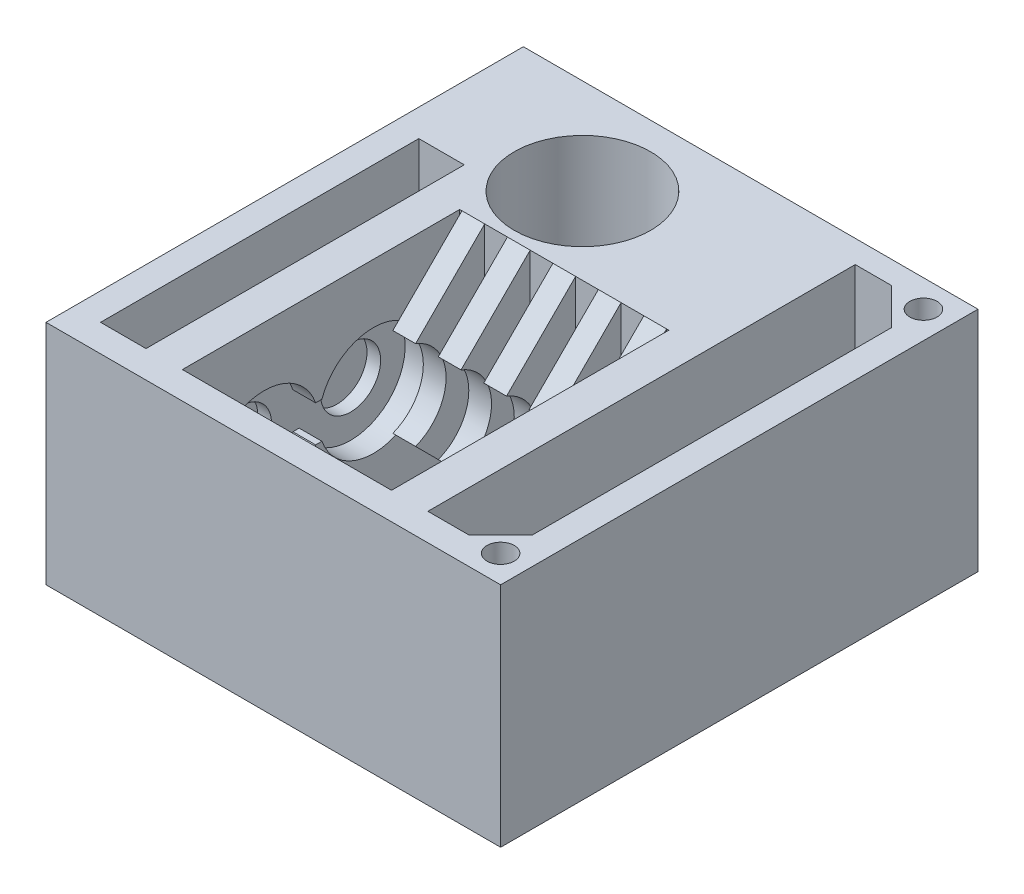
SolidWorks part; units mm, degrees
ref_plane "Front Plane" through (0, 0, 0) normal (0, 0, 1) x (1, 0, 0)
ref_plane "Top Plane" through (0, 0, 0) normal (0, 1, 0) x (1, 0, 0)
ref_plane "Right Plane" through (0, 0, 0) normal (1, 0, 0) x (0, 0, -1)
sketch "Sketch2" plane through (0, 0, 0) normal (0, 1, 0) x (1, 0, 0)
  line L0 (0, 54.9293) -> (0, -74.9036) construction
  line L1 (-50, 52.5) -> (50, 52.5)
  line L2 (-50, 52.5) -> (-50, -52.5)
  line L3 (-50, -52.5) -> (50, -52.5)
  line L4 (50, 52.5) -> (50, -52.5)
  line L5 (-72.7442, 0) -> (103.5154, 0) construction
  dimension "D1" = 105
  dimension "D2" = 100
extrude "Boss-Extrude1" add sketch "Sketch2" along normal blind 50
sketch "Sketch3" plane through (0, 50, 0) normal (0, 1, 0) x (1, 0, 0)
  line L0 (-69.2782, 0) -> (105.7343, 0) construction
  line L1 (0, 63.7563) -> (0, -72.2212) construction
  line L3 (-50, 52.5) -> (-50, -52.5) construction
  line L4 (50, 52.5) -> (-50, 52.5) construction
  circle A0 centre (-39, 0) radius 5 construction
  circle A1 centre (-39, 0) radius 39 construction
  circle A2 centre (-16.0054, 31.5) radius 15
  point P16 (-6.9479, 52.5)
  dimension "D1" = 10
  dimension "D2" = 6
  dimension "D3" = 78
  dimension "D4" = 30
  dimension "D5" = 6
  dimension "D6" = 33.9946
  dimension "D7" = 21
extrude "Cut-Extrude1" cut sketch "Sketch3" against normal up to next
sketch "Sketch5" plane through (0, 50, 0) normal (0, 1, 0) x (1, 0, 0)
  line L0 (50, -52.5) -> (50, 52.5) construction
  line L1 (28, 33.5) -> (44, 33.5)
  line L2 (28, 33.5) -> (28, -46.5)
  line L3 (28, -46.5) -> (44, -46.5)
  line L4 (44, 33.5) -> (44, -46.5)
  line L5 (-44, 23.5) -> (-34, 23.5)
  line L6 (-44, 23.5) -> (-44, -46.5)
  line L7 (-44, -46.5) -> (-34, -46.5)
  line L8 (-34, 23.5) -> (-34, -46.5)
  line L9 (-50, -52.5) -> (50, -52.5) construction
  line L10 (-50, 52.5) -> (-50, -52.5) construction
  dimension "D1" = 6
  dimension "D2" = 6
  dimension "D3" = 80
  dimension "D4" = 16
  dimension "D5" = 6
  dimension "D6" = 6
  dimension "D7" = 70
  dimension "D8" = 10
extrude "Cut-Extrude3" cut sketch "Sketch5" against normal up to next
sketch "Sketch6" plane through (28, 0, 0) normal (1, 0, 0) x (0, 0, -1)
  line L0 (-16.5, 56.9811) -> (-16.5, -19.2113) construction
  line L1 (-69.1636, 25) -> (71.5534, 25) construction
  line L2 (-17.1863, 29) -> (-15.8137, 29)
  line L3 (-17.1863, 21) -> (-15.8137, 21)
  line L4 (-46.5, 0) -> (33.5, 0)
  line L5 (33.5, 0) -> (33.5, 50)
  line L6 (33.5, 50) -> (-46.5, 50)
  line L7 (-46.5, 50) -> (-46.5, 0)
  line L8 (-46.5, 0) -> (33.5, 0) construction
  line L9 (33.5, 0) -> (33.5, 50) construction
  line L10 (33.5, 50) -> (-46.5, 50) construction
  line L11 (-46.5, 50) -> (-46.5, 0) construction
  arc A0 (-17.1863, 29) -> (-17.1863, 21) centre (-28.5, 25) ccw
  circle A2 centre (-28.5, 25) radius 9 construction
  arc A3 (-15.8137, 29) -> (-15.8137, 21) centre (-4.5, 25) cw
  arc A4 (-16.5, 25) -> (-17.1863, 29) centre (-28.5, 25) ccw construction
  arc A5 (-17.1863, 21) -> (-16.5, 25) centre (-28.5, 25) ccw construction
  arc A6 (-15.8137, 21) -> (-16.5, 25) centre (-4.5, 25) cw construction
  arc A7 (-16.5, 25) -> (-15.8137, 29) centre (-4.5, 25) cw construction
  dimension "D4" = 24
  dimension "D5" = 18
  dimension "D2" = 30
  dimension "D3" = 25
  dimension "D6" = 12
  dimension "D7" = 12
  dimension "D8" = 4
  dimension "D1" = 0
extrude "Cut-Extrude4" cut sketch "Sketch6" against normal blind 31
sketch "Sketch7" plane through (28, 0, 0) normal (1, 0, 0) x (0, 0, -1)
  line L0 (-17.1863, 21) -> (-15.8137, 21) construction
  line L1 (-15.8137, 29) -> (-17.1863, 29) construction
  line L2 (-17.1863, 21) -> (-15.8137, 21)
  line L3 (-15.8137, 29) -> (-17.1863, 29)
  arc A6 (-15.8137, 21) -> (-15.8137, 29) centre (-4.5, 25) ccw construction
  arc A7 (-17.1863, 29) -> (-17.1863, 21) centre (-28.5, 25) ccw construction
  arc A8 (-15.8137, 21) -> (-15.8137, 29) centre (-4.5, 25) ccw
  arc A9 (-17.1863, 29) -> (-17.1863, 21) centre (-28.5, 25) ccw
  circle A10 centre (-28.5, 25) radius 6.6
  circle A11 centre (-4.5, 25) radius 6.6
  dimension "D1" = 13.2
  dimension "D2" = 13.2
extrude "Boss-Extrude2" add sketch "Sketch7" against normal blind 3
ref_plane "Plane1" through (-3, 0, 0) normal (1, 0, 0) x (0, 0, -1)
mirror "Mirror1" about plane through (-3, 0, 0) normal (1, 0, 0) of "Boss-Extrude2", "Cut-Extrude4"
sketch "Sketch11" plane through (0, 50, 0) normal (0, 1, 0) x (1, 0, 0)
  line L0 (50, 52.5) -> (-50, 52.5) construction
  line L1 (28, 47.5) -> (44, 47.5)
  line L2 (28, 47.5) -> (28, 33.5)
  line L3 (28, 33.5) -> (44, 33.5)
  line L4 (44, 47.5) -> (44, 33.5)
  line L5 (44, -46.5) -> (44, 33.5) construction
  line L6 (28, 33.5) -> (28, -46.5) construction
  line L7 (44, 33.5) -> (28, 33.5) construction
  dimension "D1" = 5
extrude "Cut-Extrude7" cut sketch "Sketch11" against normal up to next
sketch "Sketch8" plane through (0, 50, 0) normal (0, 1, 0) x (1, 0, 0)
  line L0 (28, 47.5) -> (28, -46.5) construction
  line L1 (-26, 14.5) -> (20, 14.5)
  line L2 (-26, 14.5) -> (-26, -46.5)
  line L3 (-26, -46.5) -> (20, -46.5)
  line L4 (20, 14.5) -> (20, -46.5)
  line L5 (-34, -46.5) -> (-34, 23.5) construction
  line L6 (-50, -52.5) -> (50, -52.5) construction
  circle A0 centre (-16.0054, 31.5) radius 15 construction
  dimension "D4" = 2
  dimension "D1" = 8
  dimension "D2" = 8
  dimension "D3" = 6
extrude "Cut-Extrude5" cut sketch "Sketch8" against normal up to next
sketch "Sketch9" plane through (28, 0, 0) normal (1, 0, 0) x (0, 0, -1)
  line L0 (-15.8137, 29) -> (-17.1863, 29) construction
  line L1 (-17.1863, 21) -> (-15.8137, 21) construction
  line L2 (-28.5, 25) -> (60.6587, 25) construction
  line L3 (-15.8137, 29) -> (-17.1863, 29) construction
  line L4 (19.5, 55.6457) -> (19.5, -7.192) construction
  line L5 (-46.5, 0) -> (47.5, 0)
  line L6 (47.5, 0) -> (47.5, 50)
  line L7 (47.5, 50) -> (-46.5, 50)
  line L12 (-46.5, 50) -> (-46.5, 0)
  line L16 (-46.5, 50) -> (-46.5, 0) construction
  line L17 (-17.1863, 21) -> (-15.8137, 21) construction
  line L18 (52.5, 50) -> (52.5, 0) construction
  line L21 (47.5, 0) -> (47.5, 50) construction
  arc A1 (-17.1863, 29) -> (-17.1863, 21) centre (-28.5, 25) ccw construction
  circle A7 centre (19.5, 25) radius 12 construction
  arc A15 (-15.8137, 21) -> (-15.8137, 29) centre (-4.5, 25) ccw construction
  arc A16 (-17.1863, 29) -> (-17.1863, 21) centre (-28.5, 25) ccw construction
  arc A17 (-15.8137, 21) -> (-15.8137, 29) centre (-4.5, 25) ccw construction
  circle A18 centre (19.5, 25) radius 1.75
  dimension "D2" = 24
  dimension "D3" = 3.5
  dimension "D4" = 33
  dimension "D1" = 0
extrude "Cut-Extrude8" cut sketch "Sketch9" against normal blind 3
sketch "Sketch13" plane through (0, 0, 0) normal (0, -1, 0) x (1, 0, 0)
  line L0 (-62.8638, -19.5) -> (95.3177, -19.5) construction
  line L1 (5, -14.5) -> (25, -14.5)
  line L2 (5, -14.5) -> (5, -33.5)
  line L3 (5, -33.5) -> (25, -33.5)
  line L4 (25, -14.5) -> (25, -33.5)
  line L5 (50, -52.5) -> (-50, -52.5) construction
  line L6 (28, 46.5) -> (28, -47.5) construction
  dimension "D1" = 19
  dimension "D2" = 20
  dimension "D3" = 33
  dimension "D4" = 5
  dimension "D5" = 3
extrude "Cut-Extrude9" cut sketch "Sketch13" against normal blind 30
ref_plane "Plane2" through (19.5, 0, 0) normal (-1, 0, 0) x (0, 0, 1)
sketch "Sketch14" plane through (19.5, 0, 0) normal (-1, 0, 0) x (0, 0, 1)
  line L0 (-14.5, 50) -> (-14.5, 0)
  line L1 (-14.5, 0) -> (0.7085, 15.2085)
  line L2 (-19.4881, 25) -> (76.5209, 25) construction
  line L3 (-14.5, 50) -> (0.7085, 34.7915)
  line L5 (-14.5, 0) -> (46.5, 0)
  line L6 (46.5, 0) -> (46.5, 50)
  line L7 (46.5, 50) -> (-14.5, 50)
  line L8 (-14.5, 50) -> (-14.5, 30)
  line L9 (-14.5, 30) -> (-14.5, 0)
  line L10 (-14.5, 0) -> (46.5, 0) construction
  line L11 (46.5, 0) -> (46.5, 50) construction
  line L12 (46.5, 50) -> (-14.5, 50) construction
  line L13 (-14.5, 50) -> (-14.5, 30) construction
  line L14 (-14.5, 30) -> (-14.5, 0) construction
  circle A0 centre (4.5, 25) radius 6.6 construction
  circle A1 centre (4.5, 25) radius 6.6 construction
  arc A2 (0.7085, 34.7915) -> (0.7085, 15.2085) centre (4.5, 25) ccw
  circle A3 centre (28.5, 25) radius 6.6 construction
  circle A4 centre (28.5, 25) radius 6.6 construction
  circle A5 centre (28.5, 25) radius 10 construction
  arc A6 (15, 25) -> (0.7085, 34.7915) centre (4.5, 25) ccw construction
  arc A7 (0.7085, 15.2085) -> (15, 25) centre (4.5, 25) ccw construction
  dimension "D2" = 21
  dimension "D3" = 20
  dimension "D4" = 45
  dimension "D1" = 0
extrude "Boss-Extrude4" add sketch "Sketch14" along normal blind 5 separate body
pattern_linear "LPattern10" count 5 spacing 10 along (-1, 0, 0) of "Boss-Extrude4"
sketch "Sketch15" plane through (14.5, 0, 0) normal (-1, 0, 0) x (0, 0, 1)
  line L0 (46.5, 0) -> (46.5, 50) construction
  line L1 (46.5, 0) -> (46.5, 50)
  line L2 (46.5, 0) -> (31.1441, 15.3559)
  line L3 (-55.9413, 25) -> (86.0247, 25) construction
  line L4 (46.5, 50) -> (31.1441, 34.6441)
  circle A0 centre (28.5, 25) radius 6.6 construction
  circle A1 centre (28.5, 25) radius 6.6 construction
  arc A2 (31.1441, 15.3559) -> (31.1441, 34.6441) centre (28.5, 25) ccw
  arc A3 (31.1441, 34.6441) -> (18.5, 25) centre (28.5, 25) ccw construction
  arc A4 (18.5, 25) -> (31.1441, 15.3559) centre (28.5, 25) ccw construction
  dimension "D1" = 20
  dimension "D2" = 45
extrude "Boss-Extrude5" add sketch "Sketch15" along normal blind 5 separate body
pattern_linear "LPattern11" count 4 spacing 10 along (-1, 0, 0) of "Boss-Extrude5"
sketch "Sketch19" plane through (0, 50, 0) normal (0, 1, 0) x (1, 0, 0)
  line L0 (36, 47.5) -> (44, 47.5)
  line L1 (44, 47.5) -> (28, 47.5) construction
  line L2 (44, 47.5) -> (44, 39.5)
  line L3 (44, -46.5) -> (44, 47.5) construction
  line L4 (44, 39.5) -> (36, 47.5)
  dimension "D1" = 45
  dimension "D2" = 8
extrude "Boss-Extrude6" add sketch "Sketch19" against normal up to surface (50 mm away) up to face at (6, 0, -4)
mirror "Mirror2" about plane through (0, 0, 0) normal (0, 0, 1) of "Boss-Extrude6"
sketch "Sketch20" plane through (0, 50, 0) normal (0, 1, 0) x (1, 0, 0)
  line L1 (50, 52.5) -> (-50, 52.5) construction
  line L3 (50, -52.5) -> (50, 52.5) construction
  line L4 (-56.5779, 0) -> (81.0465, 0) construction
  circle A0 centre (44, 46.5) radius 3
  circle A2 centre (44, -46.5) radius 3
  dimension "D1" = 3
  dimension "D2" = 3
  dimension "D3" = 6
extrude "Cut-Extrude13" cut sketch "Sketch20" against normal up to next (50 mm away)
ref_plane "Plane3" through (0, 25, 0) normal (0, -1, 0) x (-1, 0, 0)
